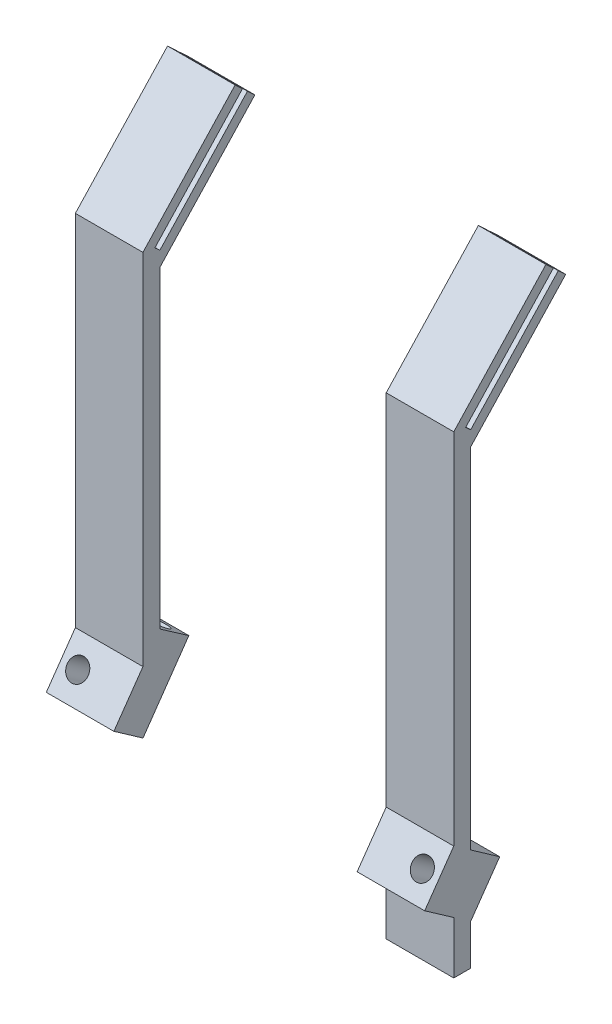
SolidWorks part; units mm, degrees
material "PET"
ref_plane "Front Plane" through (0, 0, 0) normal (0, 0, 1) x (1, 0, 0)
ref_plane "Top Plane" through (0, 0, 0) normal (0, 1, 0) x (1, 0, 0)
ref_plane "Right Plane" through (0, 0, 0) normal (1, 0, 0) x (0, 0, -1)
sketch "Sketch1" plane through (0, 0, 0) normal (1, 0, 0) x (0, 0, -1)
  line L0 (0, 0) -> (-27.2799, -29.2541)
  line L1 (-27.2799, -29.2541) -> (-27.2799, -169.2541)
  line L2 (3.6568, -3.41) -> (-22.2799, -31.2237)
  line L3 (-22.2799, -31.2237) -> (-22.2799, -169.2541)
  line L4 (0, 0) -> (3.6568, -3.41)
  line L5 (-27.2799, -169.2541) -> (-22.2799, -169.2541)
  dimension "D1" = 137
  dimension "D2" = 40
  dimension "D3" = 140
  dimension "D4" = 5
extrude "Boss-Extrude1" add sketch "Sketch1" along normal blind 20
sketch "Sketch2" plane through (20, 0, 0) normal (1, 0, 0) x (0, 0, -1)
  line L1 (-23.7426, -29.8597) -> (-22.2799, -31.2237)
  line L2 (-23.7426, -29.8597) -> (2.1941, -2.046)
  line L3 (-23.7426, -29.8597) -> (2.1941, -2.046)
  line M3 (3.6568, -3.41) -> (0, 0)
  line M8 (-22.2799, -31.2237) -> (3.6568, -3.41)
  dimension "D1" = 2
extrude "Cut-Extrude1" cut sketch "Sketch2" against normal through all and the other way through all contours L3 L1 M8 M3
sketch "Sketch3" plane through (20, 0, 0) normal (1, 0, 0) x (0, 0, -1)
  line L1 (5.8508, -5.456) -> (-20.0859, -33.2697)
  line L2 (3.6568, -3.41) -> (-22.2799, -31.2237)
  line L3 (3.6568, -3.41) -> (-22.2799, -31.2237)
  line L4 (3.6568, -3.41) -> (5.8508, -5.456)
  line L5 (-22.2799, -31.2237) -> (-20.0859, -33.2697)
  line L6 (-20.0859, -33.2697) -> (-22.2799, -35.6225)
  line L7 (-22.2799, -169.2541) -> (-22.2799, -31.2237) construction
  line L8 (-22.2799, -31.2237) -> (-22.2799, -35.6225)
  line L9 (-22.2799, -31.2237) -> (-22.2799, -35.6225)
  line M7 (-22.2799, -169.2541) -> (-22.2799, -31.2237)
  dimension "D1" = 2
  dimension "D2" = 3
extrude "Boss-Extrude2" add sketch "Sketch3" against normal up to surface (20 mm away) contours L3 L5 L1 L4 | L6 L5 M7 up to face at (0, -61.556, 17.2383)
ref_plane "Plane1" through (10, 0, 0) normal (-1, 0, 0) x (0, 0, 1)
sketch "Sketch6" plane through (0, 0, 0) normal (-1, 0, 0) x (0, 0, 1)
  line L0 (13.6763, -144.9669) -> (22.2799, -157.2541)
  line L1 (15.5819, -149.126) -> (19.0234, -154.0409) construction
  line L4 (22.2799, -169.2541) -> (22.2799, -35.6225) construction
  line L5 (13.6763, -144.9669) -> (22.2799, -138.9425)
  line L6 (17.3027, -151.5835) -> (99.2179, -94.2258) construction
  line L7 (17.9781, -151.1105) -> (42.1321, -134.1977) construction
  line L9 (27.2799, -169.2541) -> (22.2799, -169.2541) construction
  line L10 (22.2799, -138.9425) -> (22.2799, -157.2541)
  line L11 (27.2799, -135.4415) -> (35.8836, -147.7288)
  line L12 (27.2799, -29.2541) -> (27.2799, -169.2541) construction
  line L13 (35.8836, -147.7288) -> (27.2799, -153.7531)
  line L14 (22.2799, -138.9425) -> (27.2799, -135.4415)
  line L15 (22.2799, -157.2541) -> (27.2799, -153.7531)
  line L16 (27.2799, -135.4415) -> (27.2799, -153.7531)
  line M13 (22.2799, -35.6225) -> (22.2799, -169.2541)
  line M15 (27.2799, -169.2541) -> (27.2799, -29.2541)
  dimension "D1" = 12
  dimension "D2" = 15
  dimension "D3" = 15
extrude "Boss-Extrude4" add sketch "Sketch6" against normal blind 10 contours L13 L11 M15 | L5 L0 M13
sketch "Sketch7" plane through (0, -41.2669, -58.9352) normal (0, -0.5736, -0.8192) x (-1, 0, 0)
  line L0 (-5, -134.0943) -> (-5, -126.5943) construction
  line L1 (-10, -126.5943) -> (0, -126.5943) construction
  line L2 (-5, -134.0943) -> (-10, -134.0943) construction
  line L3 (-10, -126.5943) -> (-10, -141.5943) construction
  circle A0 centre (-5, -134.0943) radius 3.1
  dimension "D1" = 6.2
extrude "Cut-Extrude3" cut sketch "Sketch7" against normal through all
sketch "Sketch8" plane through (20, 0, 0) normal (1, 0, 0) x (0, 0, -1)
  line L2 (-32.1553, -151.5601) -> (82.56, 12.2703) construction
  line L4 (85.0174, 10.5496) -> (80.1025, 13.991) construction
  line L5 (-27.2799, -29.2541) -> (-27.2799, -169.2541) construction
  line L9 (-27.2799, -153.7531) -> (-22.2799, -146.6124)
  line L10 (-22.2799, -169.2541) -> (-22.2799, -35.6225) construction
  line L12 (-22.2799, -128.3008) -> (-13.6951, -134.2738)
  line L13 (-13.6951, -134.2738) -> (-22.2799, -146.6124)
  line L17 (-27.2799, -135.4415) -> (-22.2799, -128.3008)
  line L20 (-35.8836, -147.7288) -> (-27.2799, -153.7531)
  line L21 (-27.2799, -153.7531) -> (-27.2799, -135.4415)
  line L22 (-27.2799, -135.4415) -> (-35.8836, -147.7288)
  line L23 (-35.8836, -147.7288) -> (-27.2799, -153.7531)
  line L24 (-27.2799, -153.7531) -> (-27.2799, -135.4415)
  line L25 (-27.2799, -135.4415) -> (-35.8836, -147.7288)
  point P10 (-31.5818, -150.7409)
  line M12 (-27.2799, -29.2541) -> (-27.2799, -169.2541)
  line M14 (-22.2799, -169.2541) -> (-22.2799, -35.6225)
  dimension "D1" = 0
extrude "Boss-Extrude5" add sketch "Sketch8" against normal blind 10 contours L23 L2 L25 M12 | L2 L13 L12 M14 | L2 L23 L24 | L2 L12 M14
sketch "Sketch9" plane through (0, -115.9873, 81.2152) normal (0, -0.8192, 0.5736) x (-1, 0, 0)
  line L0 (-15, 60.5912) -> (-15, 55.3656) construction
  line L3 (-15, 60.5912) -> (0, 60.5912) construction
  line L4 (0, 55.3396) -> (0, 65.8427) construction
  line L5 (-10, 55.3396) -> (-10, 65.8427) construction
  line L6 (-20, 55.3396) -> (0, 55.3396) construction
  line L7 (-20, 65.8427) -> (0, 65.8427) construction
  circle A0 centre (-15, 60.5912) radius 3.1
  dimension "D1" = 6.2
  dimension "D2" = 5
extrude "Cut-Extrude4" cut sketch "Sketch9" against normal through all
ref_plane "Plane2" through (56, 0, 0) normal (1, 0, 0) x (0, 0, -1)
mirror "Mirror2" about plane through (56, 0, 0) normal (1, 0, 0) of bodies 109
sketch "Sketch11" plane through (0, 0, 0) normal (-1, 0, 0) x (0, 0, 1)
  line L0 (22.2799, -157.2541) -> (27.2799, -153.7531)
  line L33 (0, 0) -> (-2.1941, -2.046)
  line L34 (-2.1941, -2.046) -> (23.7426, -29.8597)
  line L35 (23.7426, -29.8597) -> (22.2799, -31.2237)
  line L36 (22.2799, -31.2237) -> (-3.6568, -3.41)
  line L37 (-3.6568, -3.41) -> (-5.8508, -5.456)
  line L38 (-5.8508, -5.456) -> (22.2799, -35.6225)
  line L39 (22.2799, -35.6225) -> (22.2799, -138.9425)
  line L40 (22.2799, -138.9425) -> (13.6763, -144.9669)
  line L41 (13.6763, -144.9669) -> (22.2799, -157.2541)
  line L42 (22.2799, -157.2541) -> (22.2799, -169.2541)
  line L43 (22.2799, -169.2541) -> (27.2799, -169.2541)
  line L44 (27.2799, -169.2541) -> (27.2799, -153.7531)
  line L45 (27.2799, -153.7531) -> (35.8836, -147.7288)
  line L46 (35.8836, -147.7288) -> (27.2799, -135.4415)
  line L47 (27.2799, -135.4415) -> (27.2799, -29.2541)
  line L48 (27.2799, -29.2541) -> (0, 0)
  line L49 (0, 0) -> (-2.1941, -2.046)
  line L50 (-2.1941, -2.046) -> (23.7426, -29.8597)
  line L51 (23.7426, -29.8597) -> (22.2799, -31.2237)
  line L52 (22.2799, -31.2237) -> (-3.6568, -3.41)
  line L53 (-3.6568, -3.41) -> (-5.8508, -5.456)
  line L54 (-5.8508, -5.456) -> (22.2799, -35.6225)
  line L55 (22.2799, -35.6225) -> (22.2799, -138.9425)
  line L56 (22.2799, -138.9425) -> (13.6763, -144.9669)
  line L57 (13.6763, -144.9669) -> (22.2799, -157.2541)
  line L58 (22.2799, -157.2541) -> (22.2799, -169.2541)
  line L59 (22.2799, -169.2541) -> (27.2799, -169.2541)
  line L60 (27.2799, -169.2541) -> (27.2799, -153.7531)
  line L61 (27.2799, -153.7531) -> (35.8836, -147.7288)
  line L62 (35.8836, -147.7288) -> (27.2799, -135.4415)
  line L63 (27.2799, -135.4415) -> (27.2799, -29.2541)
  line L64 (27.2799, -29.2541) -> (0, 0)
  line M26 (22.2799, -157.2541) -> (22.2799, -169.2541)
  line M27 (22.2799, -169.2541) -> (27.2799, -169.2541)
  line M28 (27.2799, -169.2541) -> (27.2799, -153.7531)
  dimension "D1" = 0
extrude "Cut-Extrude6" cut sketch "Sketch11" against normal blind 20 contours L0 M26 M27 M28
sketch "Sketch12" plane through (20, 0, 0) normal (1, 0, 0) x (0, 0, -1)
  line L0 (-22.2799, -146.6124) -> (-27.2586, -153.768)
  line L1 (-35.8836, -147.7288) -> (-22.2799, -157.2541) construction
  line L30 (-35.8836, -147.7288) -> (-22.2799, -157.2541)
  line L31 (-22.2799, -157.2541) -> (-22.2799, -146.6124)
  line L32 (-22.2799, -146.6124) -> (-13.6951, -134.2738)
  line L33 (-13.6951, -134.2738) -> (-22.2799, -128.3008)
  line L34 (-22.2799, -128.3008) -> (-22.2799, -35.6225)
  line L35 (-22.2799, -35.6225) -> (5.8508, -5.456)
  line L36 (5.8508, -5.456) -> (3.6568, -3.41)
  line L37 (3.6568, -3.41) -> (-22.2799, -31.2237)
  line L38 (-22.2799, -31.2237) -> (-23.7426, -29.8597)
  line L39 (-23.7426, -29.8597) -> (2.1941, -2.046)
  line L40 (2.1941, -2.046) -> (0, 0)
  line L41 (0, 0) -> (-27.2799, -29.2541)
  line L42 (-27.2799, -29.2541) -> (-27.2799, -135.4415)
  line L43 (-27.2799, -135.4415) -> (-35.8836, -147.7288)
  line L44 (-35.8836, -147.7288) -> (-22.2799, -157.2541)
  line L45 (-22.2799, -157.2541) -> (-22.2799, -146.6124)
  line L46 (-22.2799, -146.6124) -> (-13.6951, -134.2738)
  line L47 (-13.6951, -134.2738) -> (-22.2799, -128.3008)
  line L48 (-22.2799, -128.3008) -> (-22.2799, -35.6225)
  line L49 (-22.2799, -35.6225) -> (5.8508, -5.456)
  line L50 (5.8508, -5.456) -> (3.6568, -3.41)
  line L51 (3.6568, -3.41) -> (-22.2799, -31.2237)
  line L52 (-22.2799, -31.2237) -> (-23.7426, -29.8597)
  line L53 (-23.7426, -29.8597) -> (2.1941, -2.046)
  line L54 (2.1941, -2.046) -> (0, 0)
  line L55 (0, 0) -> (-27.2799, -29.2541)
  line L56 (-27.2799, -29.2541) -> (-27.2799, -135.4415)
  line L57 (-27.2799, -135.4415) -> (-35.8836, -147.7288)
  line M16 (-35.8836, -147.7288) -> (-22.2799, -157.2541)
  line M17 (-22.2799, -157.2541) -> (-22.2799, -146.6124)
  dimension "D1" = 0
extrude "Cut-Extrude7" cut sketch "Sketch12" against normal blind 10 contours L0 M17 M16
